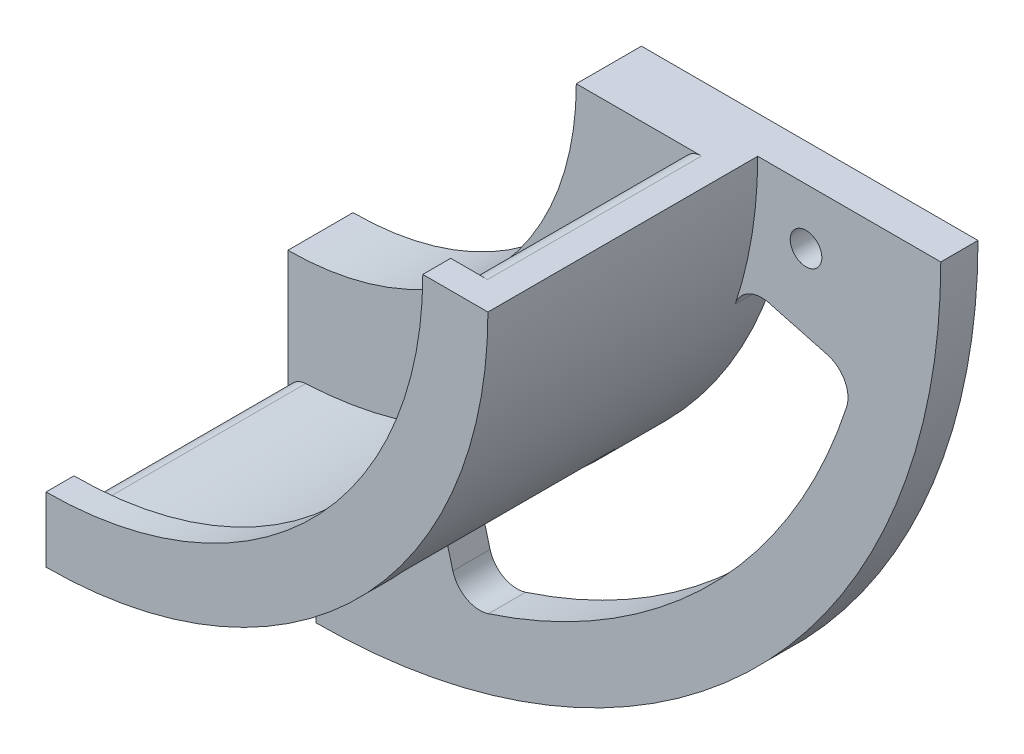
SolidWorks part; units mm, degrees
ref_plane "前视基准面" through (0, 0, 0) normal (0, 0, 1) x (1, 0, 0)
ref_plane "上视基准面" through (0, 0, 0) normal (0, 1, 0) x (1, 0, 0)
ref_plane "右视基准面" through (0, 0, 0) normal (1, 0, 0) x (0, 0, -1)
sketch "草图1" plane through (0, 0, 0) normal (0, 0, 1) x (1, 0, 0)
  line L0 (-16.68, -37.4974) -> (-16.68, -53.9974)
  line L1 (14.32, -6.4974) -> (30.82, -6.4974)
  arc A0 (-16.68, -53.9974) -> (30.82, -6.4974) centre (-16.68, -6.4974) ccw
  arc A1 (-16.68, -37.4974) -> (14.32, -6.4974) centre (-16.68, -6.4974) ccw
  dimension "D1" = 95
  dimension "D2" = 62
extrude "凸台-拉伸1" add sketch "草图1" along normal blind 3
sketch "草图2" plane through (0, 0, 3) normal (0, 0, 1) x (1, 0, 0)
  line L0 (-16.68, -48.9974) -> (-16.68, -53.9974)
  line L1 (25.82, -6.4974) -> (30.82, -6.4974)
  line L2 (13.372, -36.5495) -> (16.9076, -40.085) construction
  line L3 (15.0878, -34.7297) -> (18.6288, -38.2707)
  line L4 (11.5522, -38.2652) -> (15.0933, -41.8062)
  arc A0 (-16.68, -53.9974) -> (15.0933, -41.8062) centre (-16.68, -6.4974) ccw
  arc A1 (-16.68, -48.9974) -> (11.5522, -38.2652) centre (-16.68, -6.4974) ccw
  arc A2 (15.0878, -34.7297) -> (25.82, -6.4974) centre (-16.68, -6.4974) ccw
  arc A3 (18.6288, -38.2707) -> (30.82, -6.4974) centre (-16.68, -6.4974) ccw
  dimension "D4" = 85
  dimension "D1" = 45
  dimension "D2" = 2.5
  dimension "D3" = 2.5
extrude "凸台-拉伸2" add sketch "草图2" along normal blind 23
sketch "草图3" plane through (0, 0, 26) normal (0, 0, 1) x (1, 0, 0)
  line L0 (-16.68, -46.9974) -> (-16.68, -53.9974)
  line L1 (23.82, -6.4974) -> (30.82, -6.4974)
  arc A0 (-16.68, -53.9974) -> (30.82, -6.4974) centre (-16.68, -6.4974) ccw
  arc A1 (-16.68, -46.9974) -> (23.82, -6.4974) centre (-16.68, -6.4974) ccw
  arc A2 (15.0878, -34.7297) -> (25.82, -6.4974) centre (-16.68, -6.4974) ccw construction
  dimension "D1" = 2
extrude "凸台-拉伸3" add sketch "草图3" along normal blind 3
fillet "圆角1" radius 2 4 edges at (25.82, -6.4974, 14.5) (-16.68, -48.9974, 14.5) (11.5522, -38.2652, 14.5) (15.0878, -34.7297, 14.5)
sketch "草图4" plane through (0, 0, 0) normal (0, 0, -1) x (-1, 0, 0)
  line L0 (16.68, -6.4974) -> (-41.2755, -22.0266) construction
  line L1 (16.68, -6.4974) -> (1.1509, -64.453) construction
  line L2 (16.68, -73.6726) -> (16.68, -37.4974)
  line L3 (-41.2755, -22.0266) -> (-29.2015, -18.7913)
  line L4 (-50.4951, -6.4974) -> (-14.32, -6.4974)
  line L5 (4.3861, -52.3789) -> (1.1509, -64.453)
  circle A1 centre (10.68, -59.1873) radius 1.7
  circle A2 centre (-36.0099, -12.4974) radius 1.7
  arc A3 (-14.32, -6.4974) -> (16.68, -37.4974) centre (16.68, -6.4974) ccw
  arc A4 (-50.4951, -6.4974) -> (16.68, -73.6726) centre (16.68, -6.4974) ccw
  arc A5 (-29.2015, -18.7913) -> (4.3861, -52.3789) centre (16.68, -6.4974) ccw
  arc A6 (-41.2755, -22.0266) -> (1.1509, -64.453) centre (16.68, -6.4974) ccw
  dimension "D2" = 3.4
  dimension "D3" = 6
  dimension "D4" = 15
  dimension "D5" = 3.4
  dimension "D6" = 6
  dimension "D7" = 15
  dimension "D1" = 120
extrude "凸台-拉伸4" add sketch "草图4" along normal blind 4
fillet "圆角2" radius 3 4 edges at (41.2755, -22.0266, -2) (-1.1509, -64.453, -2) (-4.3861, -52.3789, -2) (29.2015, -18.7913, -2)
